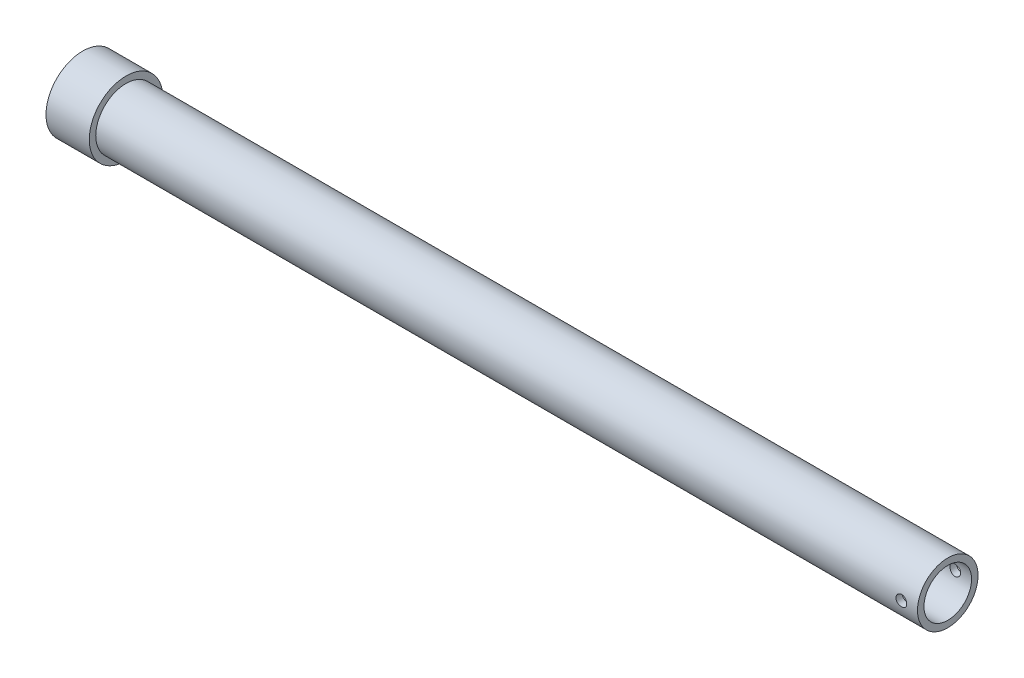
SolidWorks part; units mm, degrees
ref_plane "Front Plane" through (0, 0, 0) normal (0, 0, 1) x (1, 0, 0)
ref_plane "Top Plane" through (0, 0, 0) normal (0, 1, 0) x (1, 0, 0)
ref_plane "Right Plane" through (0, 0, 0) normal (1, 0, 0) x (0, 0, -1)
sketch "Sketch1" plane through (0, 0, 0) normal (0, 0, 1) x (1, 0, 0)
  line L1 (0, 0) -> (20, 0)
  line L2 (0, 0) -> (0, -17)
  line L3 (20, -14) -> (400, -14)
  line L4 (400, -11) -> (400, -14)
  line L7 (0, -17) -> (20, -17)
  line L8 (20, -14) -> (20, -17)
  line L10 (20, 0) -> (20, -11)
  line L11 (20, -11) -> (400, -11)
  point P11 (0, 0)
  point P12 (0, -17.5769)
  dimension "D1" = 17
  dimension "D2" = 3
  dimension "D3" = 3
  dimension "D4" = 20
  dimension "D5" = 400
revolve "Revolve1" add sketch "Sketch1" angle 360 about L1
sketch "Sketch2" plane through (0, 0, 0) normal (0, 0, 1) x (1, 0, 0)
  line L0 (400, -14) -> (400, 14) construction
  line L1 (18.7, 0) -> (-18.7, 0) construction
  circle A0 centre (392.5, 0) radius 2.5
  point P4 (0, 0)
  point P7 (0, 0)
  dimension "D1" = 5
  dimension "D2" = 7.5
extrude "Cut-Extrude1" cut sketch "Sketch2" against normal through all both and the other way through all contours A0
sketch "Sketch3" plane through (0, 0, 0) normal (-1, 0, 0) x (0, 0, 1)
  point P0 (0, 0)
